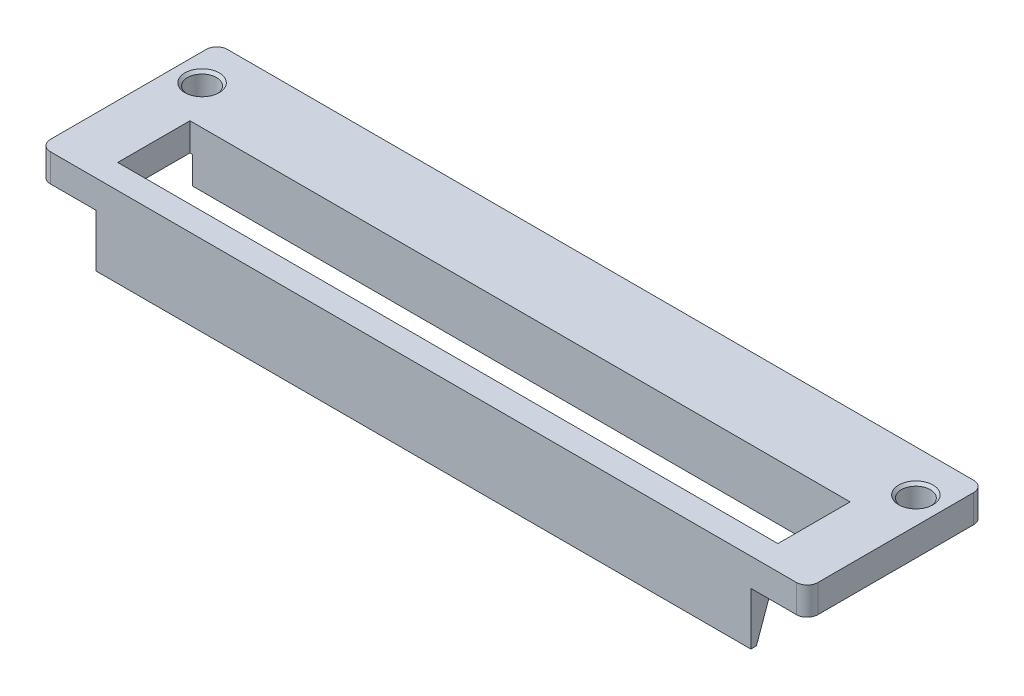
SolidWorks part; units mm, degrees
ref_plane "Front Plane" through (0, 0, 0) normal (0, 0, 1) x (1, 0, 0)
ref_plane "Top Plane" through (0, 0, 0) normal (0, 1, 0) x (1, 0, 0)
ref_plane "Right Plane" through (0, 0, 0) normal (1, 0, 0) x (0, 0, -1)
sketch "Sketch1" plane through (0, 0, 0) normal (1, 0, 0) x (0, 0, -1)
  line L0 (0, 0) -> (-7.5, 0)
  line L1 (-7.5, 0) -> (-7.5, -5.15)
  line L2 (-7.5, -5.15) -> (-6.25, -5.15)
  line L3 (-6.25, -5.15) -> (-6.25, -5.81)
  line L4 (-6.25, -5.81) -> (0, -5.81)
  line L5 (0, -5.81) -> (0, 0)
  dimension "D1" = 7.5
  dimension "D2" = 5.81
  dimension "D3" = 5.15
  dimension "D4" = 1.25
extrude "Boss-Extrude1" add sketch "Sketch1" along normal blind 71.5
sketch "Sketch2" plane through (0, 0, 0) normal (0, 1, 0) x (1, 0, 0)
  line L0 (0, 0) -> (0, -7.5) construction
  line L1 (71.5, 0) -> (71.5, -7.5) construction
  line L2 (71.5, 0) -> (0, 0) construction
  circle A0 centre (2.5, -3.875) radius 1.35
  circle A1 centre (69, -3.875) radius 1.35
  dimension "D1" = 2.7
  dimension "D2" = 2.5
  dimension "D3" = 2.5
  dimension "D4" = 3.875
extrude "Cut-Extrude1" cut sketch "Sketch2" against normal through all
sketch "Sketch3" plane through (0, 0, 0) normal (0, 1, 0) x (1, 0, 0)
  line L0 (0, -7.5) -> (0, -16.5)
  line L1 (0, -16.5) -> (71.5, -16.5)
  line L2 (71.5, -16.5) -> (71.5, -7.5)
  line L3 (71.5, -7.5) -> (66.5, -7.5)
  line L4 (71.5, -7.5) -> (0, -7.5) construction
  line L5 (66.5, -7.5) -> (66.5, -14.23)
  line L6 (66.5, -14.23) -> (5, -14.23)
  line L7 (5, -14.23) -> (5, -7.5)
  line L8 (5, -7.5) -> (0, -7.5)
  dimension "D1" = 6.73
  dimension "D2" = 2.27
  dimension "D3" = 5
extrude "Boss-Extrude2" add sketch "Sketch3" against normal blind 2.6
ref_plane "Plane2" through (5.25, 0, 0) normal (-1, 0, 0) x (0, 0, 1)
sketch "Sketch4" plane through (5.25, 0, 0) normal (-1, 0, 0) x (0, 0, 1)
  line L0 (16.5, -2.6) -> (16.5, -7.5)
  line L3 (14.23, -2.6) -> (16.5, -2.6)
  line L4 (14.23, -2.6) -> (15.98, -7.5)
  line L5 (15.98, -7.5) -> (16.5, -7.5)
  dimension "D1" = 4.9
  dimension "D2" = 0.52
extrude "Boss-Extrude3" add sketch "Sketch4" against normal blind 61
sketch "Sketch5" plane through (0, 0, 0) normal (0, 0, -1) x (-1, 0, 0)
  line L0 (-5.25, -7.5) -> (-5.25, -2.6) construction
  line L1 (0, -2.6) -> (-5.25, -2.6)
  line L2 (0, -2.6) -> (0, -5.81)
  line L3 (0, -5.81) -> (-5.25, -5.81)
  line L4 (-5.25, -2.6) -> (-5.25, -5.81)
  line L5 (-71.5, -5.81) -> (0, -5.81) construction
  line L6 (-66.25, -7.5) -> (-66.25, -2.6) construction
  line L7 (-71.5, -2.6) -> (-66.25, -2.6)
  line L8 (-71.5, -2.6) -> (-71.5, -5.81)
  line L9 (-71.5, -5.81) -> (-66.25, -5.81)
  line L10 (-66.25, -2.6) -> (-66.25, -5.81)
extrude "Cut-Extrude2" cut sketch "Sketch5" against normal through all
fillet "Fillet1" radius 1 4 edges at (71.5, -1.3, 0) (71.5, -1.3, 16.5) (0, -1.3, 16.5) (0, -1.3, 0)
chamfer "Chamfer1" distance 0.25 angle 45 2 edges at (2.5, 0, 5.225) (69, 0, 5.225)
